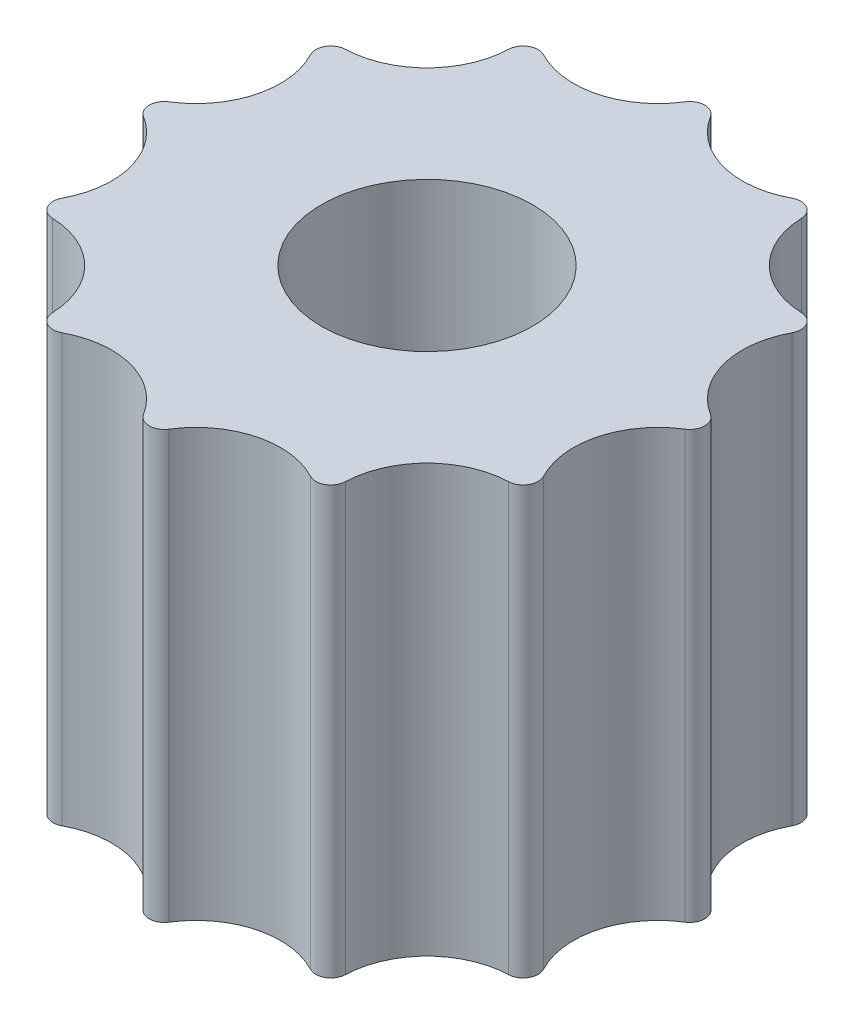
SolidWorks part; units mm, degrees
ref_plane "前视基准面" through (0, 0, 0) normal (0, 0, 1) x (1, 0, 0)
ref_plane "上视基准面" through (0, 0, 0) normal (0, 1, 0) x (1, 0, 0)
ref_plane "右视基准面" through (0, 0, 0) normal (1, 0, 0) x (0, 0, -1)
other "Configuration Table"
sketch "草图1" plane through (0, 0, 0) normal (0, 1, 0) x (1, 0, 0)
  line L0 (0, 0) -> (0, 2.7302) construction
  line L1 (0, 5.75) -> (-4.9796, 2.875) construction
  line L2 (-4.9796, 2.875) -> (-4.9796, -2.875) construction
  line L3 (-4.9796, -2.875) -> (0, -5.75) construction
  line L4 (0, -5.75) -> (4.9796, -2.875) construction
  line L5 (4.9796, -2.875) -> (4.9796, 2.875) construction
  line L6 (4.9796, 2.875) -> (0, 5.75) construction
  line L7 (0, 0) -> (-2.7003, 4.677) construction
  line L8 (0, 0) -> (-4.9796, 2.875) construction
  circle A0 centre (0, 0) radius 5.75 construction
  circle A1 centre (0, 0) radius 4.9796 construction
  circle A2 centre (0, 0) radius 2.1
  circle A3 centre (0, 0) radius 6.25 construction
  arc A4 (-3.125, 5.4127) -> (0, 6.25) centre (-1.6823, 6.2785) ccw
  arc A5 (-5.4127, 3.125) -> (-3.125, 5.4127) centre (-4.5962, 4.5962) ccw
  circle A6 centre (0, 0) radius 6.5 construction
  arc A7 (3.125, 5.4127) -> (5.4127, 3.125) centre (4.5962, 4.5962) ccw
  arc A8 (0, 6.25) -> (3.125, 5.4127) centre (1.6823, 6.2785) ccw
  arc A9 (6.25, 0) -> (5.4127, -3.125) centre (6.2785, -1.6823) ccw
  arc A10 (5.4127, 3.125) -> (6.25, 0) centre (6.2785, 1.6823) ccw
  arc A11 (3.125, -5.4127) -> (0, -6.25) centre (1.6823, -6.2785) ccw
  arc A12 (5.4127, -3.125) -> (3.125, -5.4127) centre (4.5962, -4.5962) ccw
  arc A13 (-3.125, -5.4127) -> (-5.4127, -3.125) centre (-4.5962, -4.5962) ccw
  arc A14 (0, -6.25) -> (-3.125, -5.4127) centre (-1.6823, -6.2785) ccw
  arc A15 (-6.25, 0) -> (-5.4127, 3.125) centre (-6.2785, 1.6823) ccw
  arc A16 (-5.4127, -3.125) -> (-6.25, 0) centre (-6.2785, -1.6823) ccw
  point P47 (0, 0)
  dimension "D1" = 11.5
  dimension "D2" = 4.2
  dimension "D3" = 12.5
  dimension "D4" = 30
  dimension "D5" = 13
  dimension "D6" = 6
extrude "凸台-拉伸1" add sketch "草图1" along normal blind 8.5
fillet "圆角1" radius 0.3 12 edges at (5.4127, 4.25, -3.125) (6.25, 4.25, 0) (5.4127, 4.25, 3.125) (3.125, 4.25, 5.4127) (0, 4.25, 6.25) (-3.125, 4.25, 5.4127) (-5.4127, 4.25, 3.125) (-6.25, 4.25, 0) (-5.4127, 4.25, -3.125) (-3.125, 4.25, -5.4127) (0, 4.25, -6.25) (3.125, 4.25, -5.4127)
